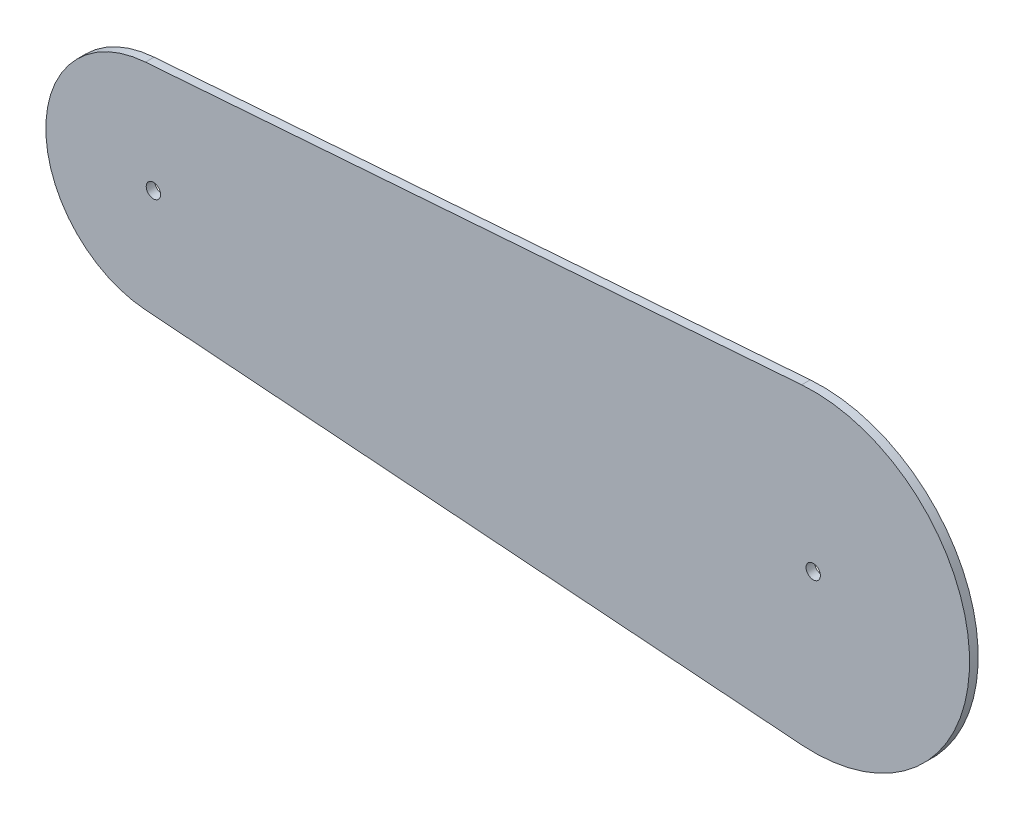
SolidWorks part; units mm, degrees
ref_plane "Front Plane" through (0, 0, 0) normal (0, 0, 1) x (1, 0, 0)
ref_plane "Top Plane" through (0, 0, 0) normal (0, 1, 0) x (1, 0, 0)
ref_plane "Right Plane" through (0, 0, 0) normal (1, 0, 0) x (0, 0, -1)
sketch "Sketch1" plane through (0, 0, 0) normal (0, 0, 1) x (1, 0, 0)
  line L0 (2.5, 0) -> (227.5, 0) construction
  line L1 (-2.5, 0) -> (-37.5, 0) construction
  line L2 (232.5, 0) -> (284.5, 0) construction
  line L3 (-2.7717, 37.3974) -> (225.9717, 54.3509)
  line L4 (-2.7717, -37.3974) -> (225.9717, -54.3509)
  circle A0 centre (0, 0) radius 2.5
  circle A1 centre (0, 0) radius 37.5
  circle A2 centre (230, 0) radius 2.5
  circle A3 centre (230, 0) radius 54.5
  dimension "D1" = 225
  dimension "D2" = 5
  dimension "D3" = 5
  dimension "D4" = 35
  dimension "D5" = 52
extrude "Boss-Extrude1" add sketch "Sketch1" along normal blind 3 contours A1 A0 | A3 L3 A1 L4 | A3 A2
